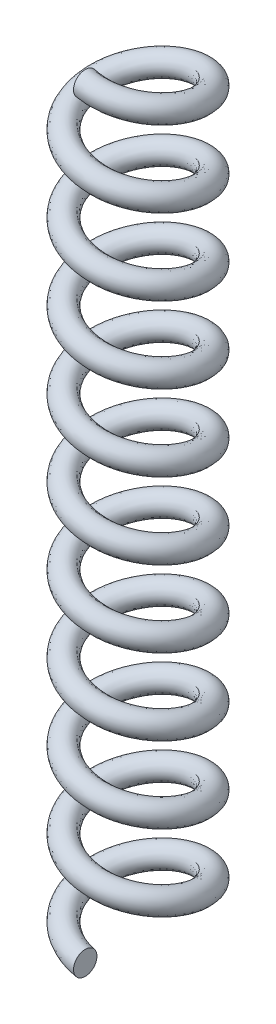
SolidWorks part; units mm, degrees
ref_plane "前视基准面" through (0, 0, 0) normal (0, 0, 1) x (1, 0, 0)
ref_plane "上视基准面" through (0, 0, 0) normal (0, 1, 0) x (1, 0, 0)
ref_plane "右视基准面" through (0, 0, 0) normal (1, 0, 0) x (0, 0, -1)
sketch "草图1" plane through (0, 0, 0) normal (0, 1, 0) x (1, 0, 0)
  circle A0 centre (0, 0) radius 4.5
  dimension "D1" = 9
curve "螺旋线/涡状线1" pitch 6.5 height 65 turns 10
sketch "草图2" plane through (0, 0, 0) normal (1, 0, 0) x (0, 0, -1)
  circle A0 centre (-4.5, 0) radius 1
  spline S0 degree 3 poles (-4.5, 0) (-4.5, 0.1346) (-4.2657, 0.4066) (-3.2648, 0.8124) (-1.7669, 1.2188) (0, 1.625) (1.7669, 2.0313) (3.2648, 2.4375) (4.2657, 2.8438) (4.6172, 3.25) (4.2657, 3.6563) (3.2648, 4.0625) (1.2676, 4.6042) (-1.2676, 5.1458) (-3.2648, 5.6875) (-4.2657, 6.0938) (-4.6172, 6.5) (-4.2657, 6.9063) (-3.2648, 7.3125) (-1.2676, 7.8542) (1.2676, 8.3958) (3.2648, 8.9375) (4.2657, 9.3438) (4.6172, 9.75) (4.2657, 10.1563) (3.2648, 10.5625) (1.2676, 11.1042) (-1.2676, 11.6458) (-3.2648, 12.1875) (-4.2657, 12.5938) (-4.6172, 13) (-4.2657, 13.4063) (-3.2648, 13.8125) (-1.2676, 14.3542) (1.2676, 14.8958) (3.2648, 15.4375) (4.2657, 15.8438) (4.6172, 16.25) (4.2657, 16.6563) (3.2648, 17.0625) (1.2676, 17.6042) (-1.2676, 18.1458) (-3.2648, 18.6875) (-4.2657, 19.0938) (-4.6172, 19.5) (-4.2657, 19.9063) (-3.2648, 20.3125) (-1.2676, 20.8542) (1.2676, 21.3958) (3.2648, 21.9375) (4.2657, 22.3438) (4.6172, 22.75) (4.2657, 23.1563) (3.2648, 23.5625) (1.2676, 24.1042) (-1.2676, 24.6458) (-3.2648, 25.1875) (-4.2657, 25.5938) (-4.6172, 26) (-4.2657, 26.4063) (-3.2648, 26.8125) (-1.2676, 27.3542) (1.2676, 27.8958) (3.2648, 28.4375) (4.2657, 28.8438) (4.6172, 29.25) (4.2657, 29.6563) (3.2648, 30.0625) (1.2676, 30.6042) (-1.2676, 31.1458) (-3.2648, 31.6875) (-4.2657, 32.0938) (-4.6172, 32.5) (-4.2657, 32.9063) (-3.2648, 33.3125) (-1.2676, 33.8542) (1.2676, 34.3958) (3.2648, 34.9375) (4.2657, 35.3438) (4.6172, 35.75) (4.2657, 36.1562) (3.2648, 36.5625) (1.2676, 37.1042) (-1.2676, 37.6458) (-3.2648, 38.1875) (-4.2657, 38.5937) (-4.6172, 39) (-4.2657, 39.4062) (-3.2648, 39.8125) (-1.2676, 40.3542) (1.2676, 40.8958) (3.2648, 41.4375) (4.2657, 41.8437) (4.6172, 42.25) (4.2657, 42.6562) (3.2648, 43.0625) (1.2676, 43.6042) (-1.2676, 44.1458) (-3.2648, 44.6875) (-4.2657, 45.0937) (-4.6172, 45.5) (-4.2657, 45.9062) (-3.2648, 46.3125) (-1.2676, 46.8542) (1.2676, 47.3958) (3.2648, 47.9375) (4.2657, 48.3437) (4.6172, 48.75) (4.2657, 49.1562) (3.2648, 49.5625) (1.2676, 50.1042) (-1.2676, 50.6458) (-3.2648, 51.1875) (-4.2657, 51.5937) (-4.6172, 52) (-4.2657, 52.4062) (-3.2648, 52.8125) (-1.2676, 53.3542) (1.2676, 53.8958) (3.2648, 54.4375) (4.2657, 54.8437) (4.6172, 55.25) (4.2657, 55.6562) (3.2648, 56.0625) (1.2676, 56.6042) (-1.2676, 57.1458) (-3.2648, 57.6875) (-4.2657, 58.0937) (-4.6172, 58.5) (-4.2657, 58.9062) (-3.2648, 59.3125) (-1.2676, 59.8542) (1.2676, 60.3958) (3.2648, 60.9375) (4.2657, 61.3437) (4.6172, 61.75) (4.2657, 62.1562) (3.2648, 62.5625) (1.7669, 62.9687) (0, 63.375) (-1.7669, 63.7812) (-3.2648, 64.1876) (-4.2657, 64.5934) (-4.5, 64.8654) (-4.5, 65) knots 0 0 0 0 0.00625 0.0125 0.01875 0.025 0.03125 0.0375 0.04375 0.05 0.05625 0.0625 0.06875 0.08125 0.0875 0.09375 0.1 0.10625 0.1125 0.11875 0.13125 0.1375 0.14375 0.15 0.15625 0.1625 0.16875 0.18125 0.1875 0.19375 0.2 0.20625 0.2125 0.21875 0.23125 0.2375 0.24375 0.25 0.25625 0.2625 0.26875 0.28125 0.2875 0.29375 0.3 0.30625 0.3125 0.31875 0.33125 0.3375 0.34375 0.35 0.35625 0.3625 0.36875 0.38125 0.3875 0.39375 0.4 0.40625 0.4125 0.41875 0.43125 0.4375 0.44375 0.45 0.45625 0.4625 0.46875 0.48125 0.4875 0.49375 0.5 0.50625 0.5125 0.51875 0.53125 0.5375 0.54375 0.55 0.55625 0.5625 0.56875 0.58125 0.5875 0.59375 0.6 0.60625 0.6125 0.61875 0.63125 0.6375 0.64375 0.65 0.65625 0.6625 0.66875 0.68125 0.6875 0.69375 0.7 0.70625 0.7125 0.71875 0.73125 0.7375 0.74375 0.75 0.75625 0.7625 0.76875 0.78125 0.7875 0.79375 0.8 0.80625 0.8125 0.81875 0.83125 0.8375 0.84375 0.85 0.85625 0.8625 0.86875 0.88125 0.8875 0.89375 0.9 0.90625 0.9125 0.91875 0.93125 0.9375 0.94375 0.95 0.95625 0.9625 0.96875 0.975 0.98125 0.9875 0.99375 1 1 1 1 construction
  dimension "D1" = 2
sweep "扫描1" add profiles "草图2" path "螺旋线/涡状线1"
sketch "草图3" plane through (0, 0, 0) normal (0, 1, 0) x (1, 0, 0)
  circle A0 centre (0, 0) radius 12.444 construction
